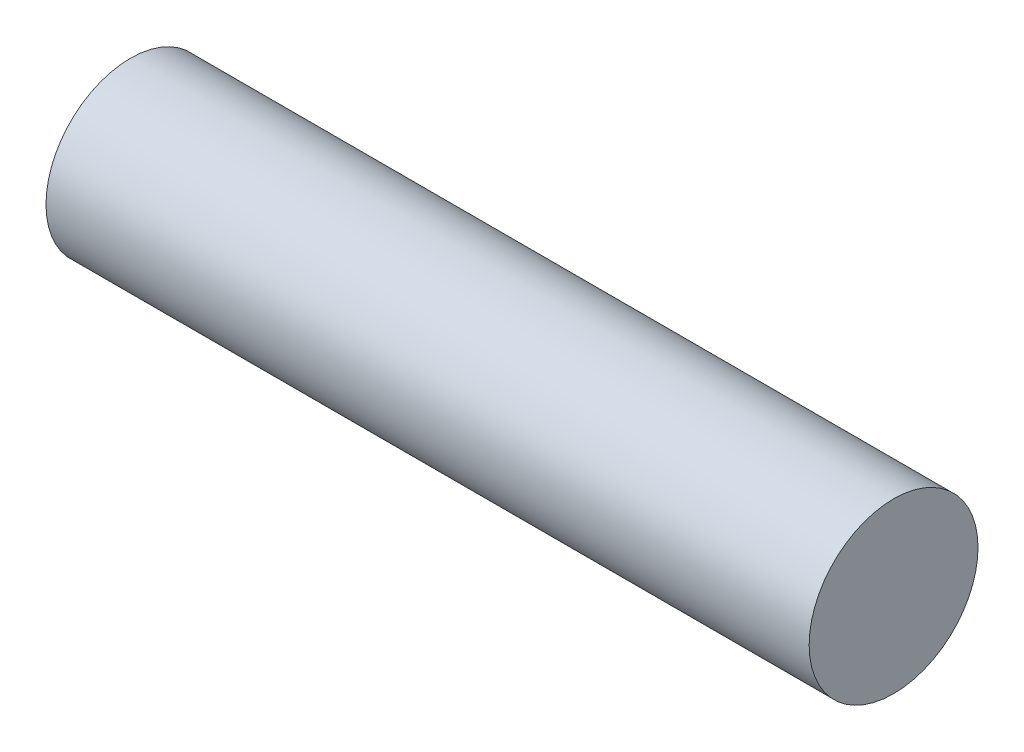
SolidWorks part; units mm, degrees
ref_plane "Front Plane" through (0, 0, 0) normal (0, 0, 1) x (1, 0, 0)
ref_plane "Top Plane" through (0, 0, 0) normal (0, 1, 0) x (1, 0, 0)
ref_plane "Right Plane" through (0, 0, 0) normal (1, 0, 0) x (0, 0, -1)
sketch "Sketch1" plane through (0, 0, 0) normal (1, 0, 0) x (0, 0, -1)
  circle A0 centre (0, 0) radius 3.175
  dimension "D1" = 6.35
extrude "main" add sketch "Sketch1" along normal mid plane 28.702
